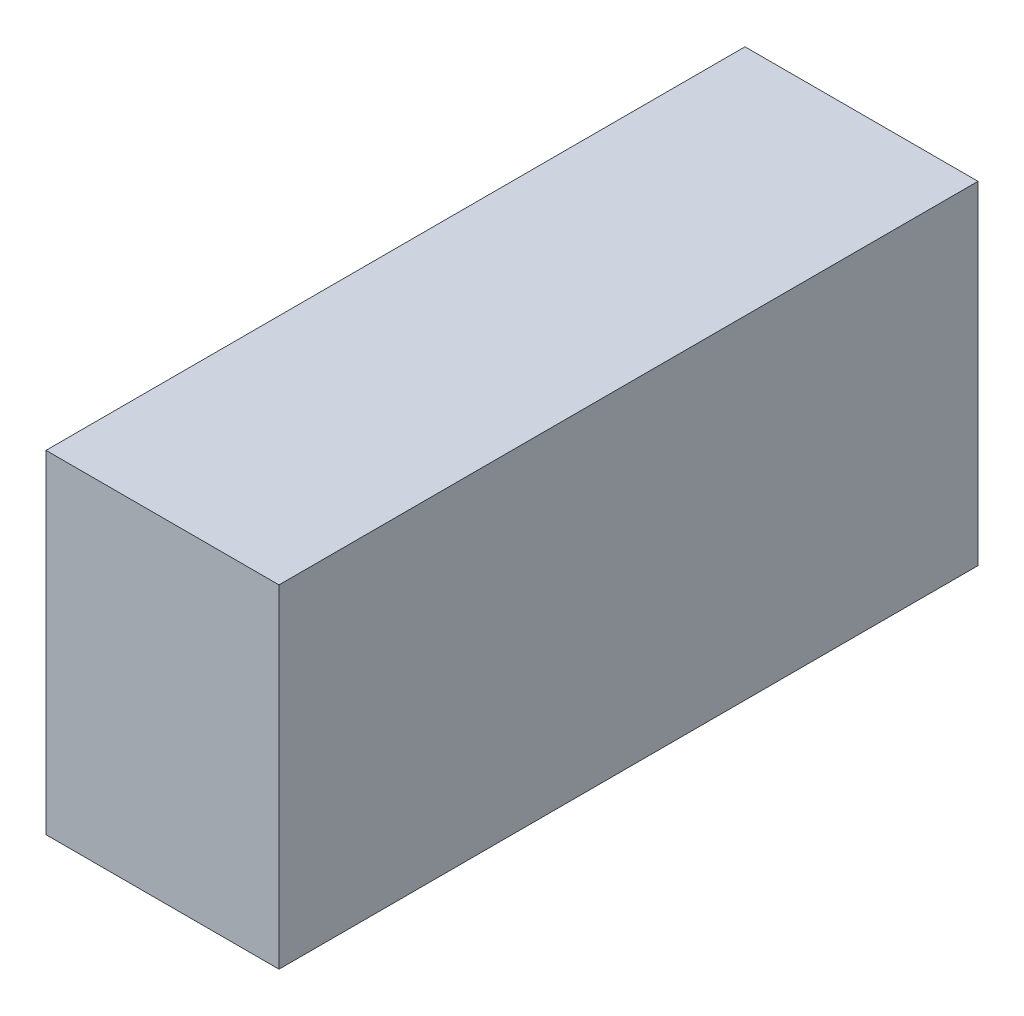
SolidWorks part; units mm, degrees
ref_plane "Front Plane" through (0, 0, 0) normal (0, 0, 1) x (1, 0, 0)
ref_plane "Top Plane" through (0, 0, 0) normal (0, 1, 0) x (1, 0, 0)
ref_plane "Right Plane" through (0, 0, 0) normal (1, 0, 0) x (0, 0, -1)
sketch "Sketch2" plane through (0, 0, 0) normal (0, 1, 0) x (1, 0, 0)
  line L1 (0, 0) -> (22.225, 0)
  line L2 (0, 0) -> (0, 66.675)
  line L3 (0, 66.675) -> (22.225, 66.675)
  line L4 (22.225, 0) -> (22.225, 66.675)
  dimension "D1" = 66.675
  dimension "D2" = 22.225
extrude "Boss-Extrude1" add sketch "Sketch2" along normal blind 31.75
